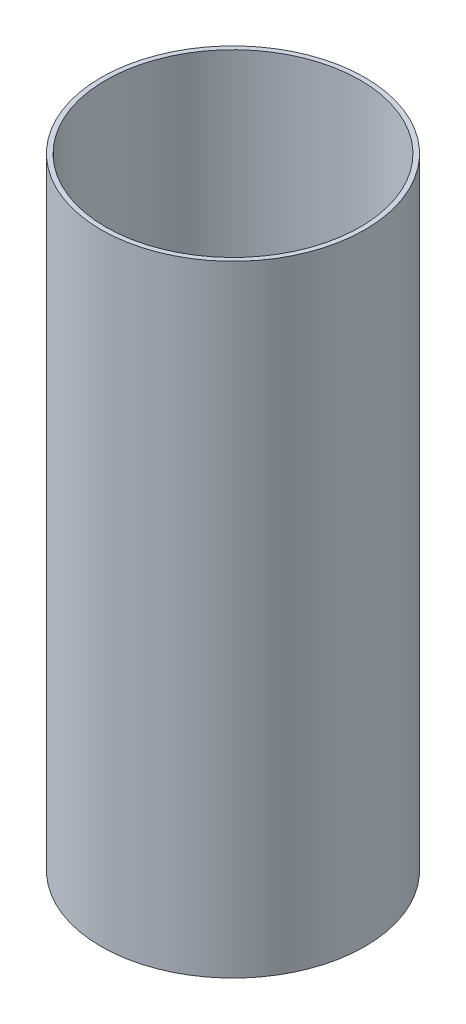
SolidWorks part; units mm, degrees
ref_plane "Front Plane" through (0, 0, 0) normal (0, 0, 1) x (1, 0, 0)
ref_plane "Top Plane" through (0, 0, 0) normal (0, 1, 0) x (1, 0, 0)
ref_plane "Right Plane" through (0, 0, 0) normal (1, 0, 0) x (0, 0, -1)
sketch "Sketch1" plane through (0, 0, 0) normal (0, 1, 0) x (1, 0, 0)
  circle A0 centre (0, 0) radius 42.5
  circle A1 centre (0, 0) radius 41
  dimension "D1" = 1.5
  dimension "D2" = 82
extrude "Boss-Extrude1" add sketch "Sketch1" along normal blind 200
